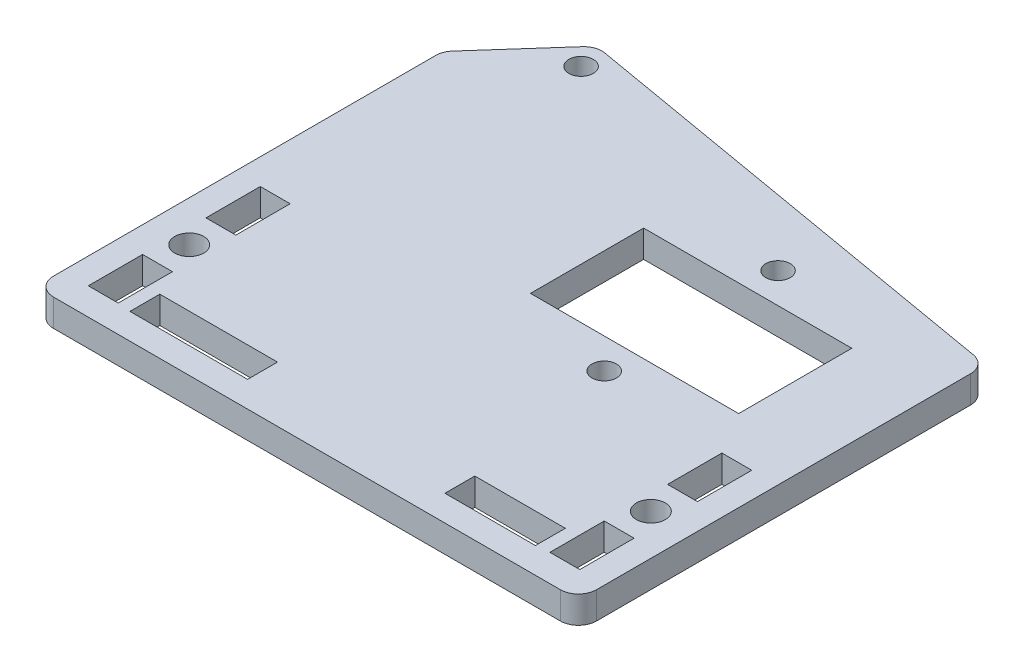
SolidWorks part; units mm, degrees
ref_plane "Front Plane" through (0, 0, 0) normal (0, 0, 1) x (1, 0, 0)
ref_plane "Top Plane" through (0, 0, 0) normal (0, 1, 0) x (1, 0, 0)
ref_plane "Right Plane" through (0, 0, 0) normal (1, 0, 0) x (0, 0, -1)
sketch "Sketch1" plane through (0, 0, 0) normal (0, 1, 0) x (1, 0, 0)
  line L0 (58.3411, 45.2871) -> (9.0966, 53.8102)
  line L1 (2, 0) -> (58, 0)
  line L2 (0, 2) -> (0, 44.2396)
  line L4 (60, 2) -> (60, 43.3164)
  line L5 (7.2607, 53.1682) -> (0.5052, 45.5683)
  arc A0 (2, 0) -> (0, 2) centre (2, 2) cw
  arc A1 (58, 0) -> (60, 2) centre (58, 2) ccw
  arc A2 (58.3411, 45.2871) -> (60, 43.3164) centre (58, 43.3164) cw
  arc A3 (0, 44.2396) -> (0.5052, 45.5683) centre (2, 44.2396) cw
  arc A4 (9.0966, 53.8102) -> (7.2607, 53.1682) centre (8.7555, 51.8395) ccw
  point P8 (0, 0)
  point P11 (60, 0)
  point P14 (60, 45)
  point P17 (0, 45)
  point P20 (8, 54)
  dimension "D6" = 2
  dimension "D1" = 60
  dimension "D2" = 54
  dimension "D3" = 8
  dimension "D4" = 45
  dimension "D5" = 45
extrude "Boss-Extrude1" add sketch "Sketch1" along normal blind 3
sketch "Sketch2" plane through (0, 3, 0) normal (0, 1, 0) x (1, 0, 0)
  line L0 (0, 44.2396) -> (0, 2) construction
  line L1 (3, 3) -> (6, 3)
  line L2 (3, 3) -> (3, 9)
  line L3 (3, 9) -> (6, 9)
  line L4 (6, 3) -> (6, 9)
  line L5 (3, 16) -> (6, 16)
  line L6 (3, 16) -> (3, 22)
  line L7 (3, 22) -> (6, 22)
  line L8 (6, 16) -> (6, 22)
  line L9 (54, 3) -> (57, 3)
  line L10 (54, 3) -> (54, 9)
  line L11 (54, 9) -> (57, 9)
  line L12 (57, 3) -> (57, 9)
  line L13 (54, 16) -> (57, 16)
  line L14 (54, 16) -> (54, 22)
  line L15 (54, 22) -> (57, 22)
  line L16 (57, 16) -> (57, 22)
  line L17 (7.6, 6) -> (20.6, 6)
  line L18 (7.6, 6) -> (7.6, 3)
  line L19 (7.6, 3) -> (20.6, 3)
  line L20 (20.6, 6) -> (20.6, 3)
  line L21 (42.4, 6) -> (52.4, 6)
  line L22 (42.4, 6) -> (42.4, 3)
  line L23 (42.4, 3) -> (52.4, 3)
  line L24 (52.4, 6) -> (52.4, 3)
  line L25 (28, 39.2) -> (51, 39.2)
  line L26 (28, 39.2) -> (28, 26.7)
  line L27 (28, 26.7) -> (51, 26.7)
  line L28 (51, 39.2) -> (51, 26.7)
  line L29 (60, 2) -> (60, 43.3164) construction
  line L30 (2, 0) -> (58, 0) construction
  line L31 (39.5, 23.35) -> (39.5, 26.7) construction
  line L32 (39.5, 42.55) -> (39.5, 39.2) construction
  line L33 (55.5, 16) -> (55.5, 9) construction
  line L34 (4.5, 16) -> (4.5, 9) construction
  circle A0 centre (9.0799, 51.2129) radius 1.35
  circle A1 centre (39.5, 42.55) radius 1.35
  circle A2 centre (39.5, 23.35) radius 1.35
  circle A3 centre (55.5, 12.5) radius 1.6
  circle A4 centre (4.5, 12.5) radius 1.6
  point P47 (4.5, 12.5)
  dimension "D9" = 2.7
  dimension "D11" = 3.2
  dimension "D1" = 3
  dimension "D2" = 3
  dimension "D3" = 3
  dimension "D4" = 6
  dimension "D5" = 23
  dimension "D6" = 12.5
  dimension "D7" = 9
  dimension "D8" = 26.7
  dimension "D10" = 3.35
  dimension "D12" = 3
  dimension "D13" = 7
  dimension "D14" = 3
  dimension "D15" = 10
  dimension "D16" = 13
  dimension "D17" = 3
  dimension "D18" = 1.6
  dimension "D19" = 1.6
extrude "Main Holes" cut sketch "Sketch2" against normal through all
sketch "Sketch3" plane through (0, 3, 0) normal (0, 1, 0) x (1, 0, 0)
  line L0 (3, 16) -> (6, 16) construction
  line L1 (6, 22) -> (6.15, 22)
  line L2 (6, 22) -> (6, 16)
  line L3 (6, 16) -> (6.15, 16)
  line L4 (6.15, 22) -> (6.15, 16)
  line L5 (3, 22) -> (2.85, 22)
  line L6 (3, 22) -> (3, 16)
  line L7 (3, 16) -> (2.85, 16)
  line L8 (2.85, 22) -> (2.85, 16)
  line L9 (6, 9) -> (6.15, 9)
  line L10 (6, 9) -> (6, 3)
  line L11 (6, 3) -> (6.15, 3)
  line L12 (6.15, 9) -> (6.15, 3)
  line L13 (3, 9) -> (2.85, 9)
  line L14 (3, 9) -> (3, 3)
  line L15 (3, 3) -> (2.85, 3)
  line L16 (2.85, 9) -> (2.85, 3)
  line L17 (57, 9) -> (57.15, 9)
  line L18 (57, 9) -> (57, 3)
  line L19 (57, 3) -> (57.15, 3)
  line L20 (57.15, 9) -> (57.15, 3)
  line L21 (54, 9) -> (53.85, 9)
  line L22 (54, 9) -> (54, 3)
  line L23 (54, 3) -> (53.85, 3)
  line L24 (53.85, 9) -> (53.85, 3)
  line L25 (57, 22) -> (57.15, 22)
  line L26 (57, 22) -> (57, 16)
  line L27 (57, 16) -> (57.15, 16)
  line L28 (57.15, 22) -> (57.15, 16)
  line L29 (54, 22) -> (53.85, 22)
  line L30 (54, 22) -> (54, 16)
  line L31 (54, 16) -> (53.85, 16)
  line L32 (53.85, 22) -> (53.85, 16)
  line L33 (52.4, 6) -> (42.4, 6)
  line L34 (52.4, 6) -> (52.4, 6.15)
  line L35 (52.4, 6.15) -> (42.4, 6.15)
  line L36 (42.4, 6) -> (42.4, 6.15)
  line L37 (52.4, 3) -> (42.4, 3)
  line L38 (52.4, 3) -> (52.4, 2.85)
  line L39 (52.4, 2.85) -> (42.4, 2.85)
  line L40 (42.4, 3) -> (42.4, 2.85)
  line L41 (7.6, 6) -> (20.6, 6)
  line L42 (7.6, 6) -> (7.6, 6.15)
  line L43 (7.6, 6.15) -> (20.6, 6.15)
  line L44 (20.6, 6) -> (20.6, 6.15)
  line L45 (7.6, 3) -> (20.6, 3)
  line L46 (7.6, 3) -> (7.6, 2.85)
  line L47 (7.6, 2.85) -> (20.6, 2.85)
  line L48 (20.6, 3) -> (20.6, 2.85)
  line L49 (3, 3) -> (6, 3) construction
  line L50 (54, 16) -> (57, 16) construction
  line L51 (54, 3) -> (57, 3) construction
  line L52 (42.4, 6) -> (42.4, 3) construction
  line L53 (20.6, 3) -> (20.6, 6) construction
  dimension "D1" = 0.15
  dimension "D2" = 0.15
  dimension "D3" = 0.15
extrude "Tolerance" cut sketch "Sketch3" against normal through all
